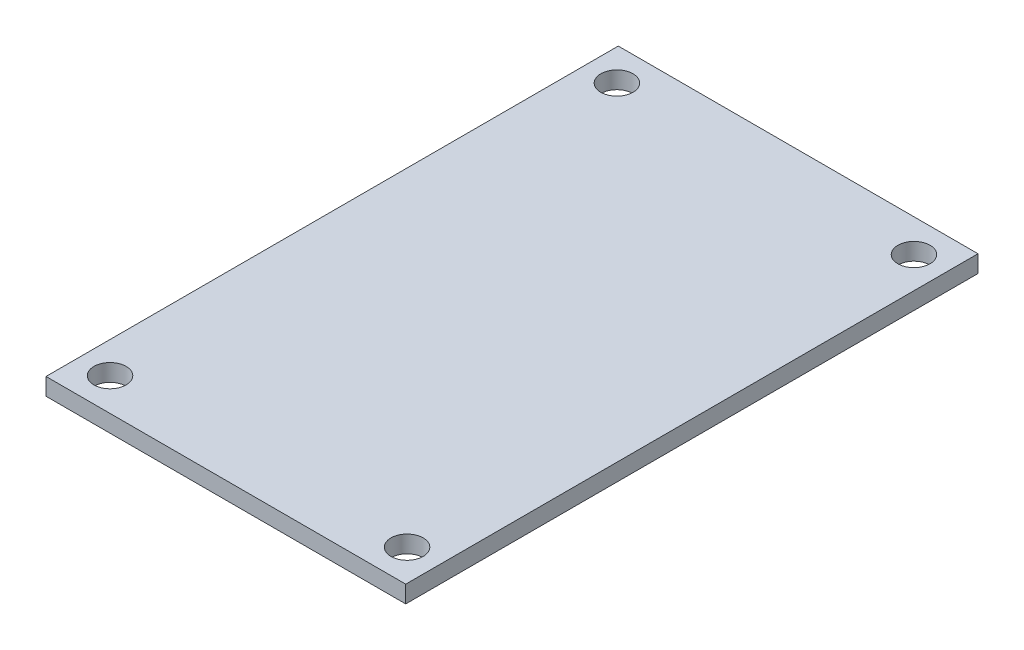
SolidWorks part; units mm, degrees
ref_plane "Front Plane" through (0, 0, 0) normal (0, 0, 1) x (1, 0, 0)
ref_plane "Top Plane" through (0, 0, 0) normal (0, 1, 0) x (1, 0, 0)
ref_plane "Right Plane" through (0, 0, 0) normal (1, 0, 0) x (0, 0, -1)
sketch "Sketch1" plane through (0, 0, 0) normal (0, 1, 0) x (1, 0, 0)
  line L0 (16.764, 0) -> (-16.764, 0) construction
  line L1 (16.764, -26.67) -> (-16.764, -26.67)
  line L2 (16.764, -26.67) -> (16.764, 26.67)
  line L3 (16.764, 26.67) -> (-16.764, 26.67)
  line L4 (-16.764, -26.67) -> (-16.764, 26.67)
  line L5 (16.764, -26.67) -> (-16.764, 26.67) construction
  line L6 (16.764, 26.67) -> (-16.764, -26.67) construction
  line L7 (0, -26.67) -> (0, 26.67) construction
  circle A0 centre (-13.843, 23.622) radius 1.5
  circle A3 centre (13.843, 23.622) radius 1.5
  circle A4 centre (13.843, -23.622) radius 1.5
  circle A5 centre (-13.843, -23.622) radius 1.5
  point P0 (0, 0)
  point P9 (0, 0)
  point P12 (0, 0)
  dimension "D4" = 3
  dimension "D1" = 53.34
  dimension "D2" = 33.528
  dimension "D3" = 2.921
  dimension "D5" = 3.048
extrude "Boss-Extrude1" add sketch "Sketch1" along normal blind 1.6
